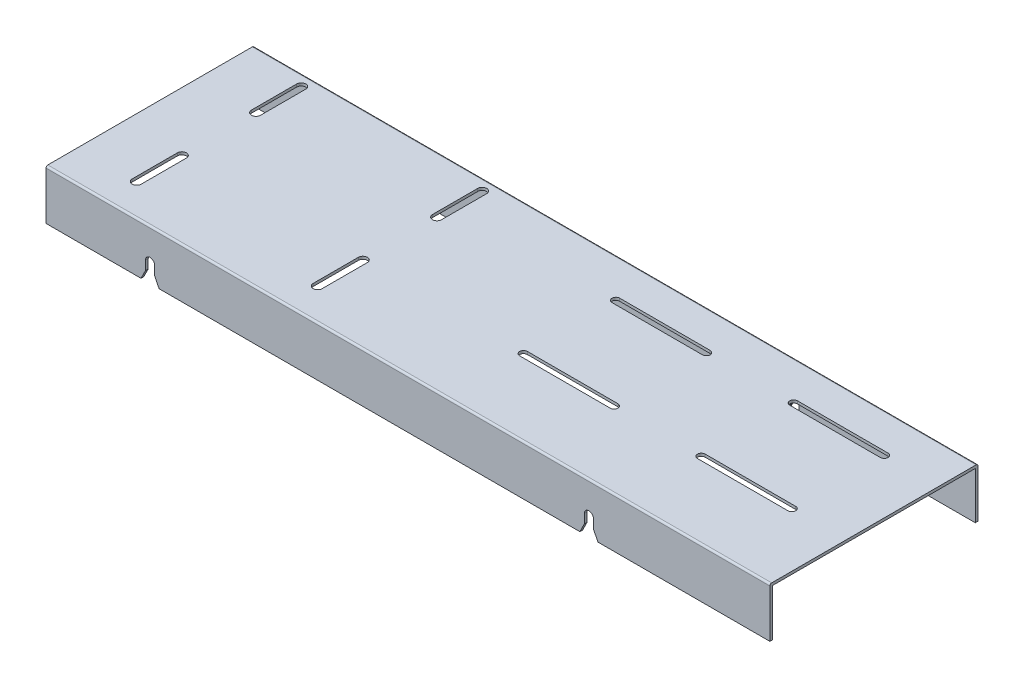
SolidWorks part; units mm, degrees
ref_plane "Plan de face" through (0, 0, 0) normal (0, 0, 1) x (1, 0, 0)
ref_plane "Plan de dessus" through (0, 0, 0) normal (0, 1, 0) x (1, 0, 0)
ref_plane "Plan de droite" through (0, 0, 0) normal (1, 0, 0) x (0, 0, -1)
sketch "Esquisse1" plane through (0, 0, 0) normal (1, 0, 0) x (0, 0, -1)
  line L0 (0, 0) -> (230, 0)
  line L1 (230, 0) -> (230, -55)
  line L2 (230, -55) -> (227, -55)
  line L3 (227, -55) -> (227, -3)
  line L4 (227, -3) -> (3, -3)
  line L5 (3, -3) -> (3, -55)
  line L6 (3, -55) -> (0, -55)
  line L7 (0, -55) -> (0, 0)
  dimension "D1" = 224
  dimension "D2" = 3
  dimension "D3" = 3
  dimension "D4" = 3
  dimension "D5" = 55
  dimension "D6" = 55
extrude "Boss.-Extru.1" add sketch "Esquisse1" along normal blind 800
sketch "Esquisse2" plane through (0, 0, 0) normal (0, 1, 0) x (1, 0, 0)
  line L0 (443.5, 186.25) -> (543.5, 186.25) construction
  line L1 (443.5, 190.5) -> (543.5, 190.5)
  line L2 (443.5, 182) -> (543.5, 182)
  line L3 (640, 186.25) -> (740, 186.25) construction
  line L4 (640, 190.5) -> (740, 190.5)
  line L5 (640, 182) -> (740, 182)
  line L6 (443.5, 84.25) -> (543.5, 84.25) construction
  line L7 (443.5, 88.5) -> (543.5, 88.5)
  line L8 (443.5, 80) -> (543.5, 80)
  line L9 (640, 84.25) -> (740, 84.25) construction
  line L10 (640, 88.5) -> (740, 88.5)
  line L11 (640, 80) -> (740, 80)
  line L12 (800, 230) -> (800, 0) construction
  line L13 (800, 0) -> (0, 0) construction
  arc A0 (443.5, 190.5) -> (443.5, 182) centre (443.5, 186.25) ccw
  arc A1 (543.5, 182) -> (543.5, 190.5) centre (543.5, 186.25) ccw
  arc A2 (640, 190.5) -> (640, 182) centre (640, 186.25) ccw
  arc A3 (740, 182) -> (740, 190.5) centre (740, 186.25) ccw
  arc A4 (443.5, 88.5) -> (443.5, 80) centre (443.5, 84.25) ccw
  arc A5 (543.5, 80) -> (543.5, 88.5) centre (543.5, 84.25) ccw
  arc A6 (640, 88.5) -> (640, 80) centre (640, 84.25) ccw
  arc A7 (740, 80) -> (740, 88.5) centre (740, 84.25) ccw
  point P2 (493.5, 186.25)
  point P7 (690, 186.25)
  point P14 (493.5, 84.25)
  point P21 (690, 84.25)
  dimension "D1" = 4.25
  dimension "D8" = 4.25
  dimension "D9" = 4.25
  dimension "D2" = 4.25
  dimension "D3" = 100
  dimension "D4" = 100
  dimension "D5" = 100
  dimension "D6" = 100
  dimension "D7" = 196.5
  dimension "D10" = 196.5
  dimension "D11" = 196.5
  dimension "D12" = 196.5
  dimension "D13" = 60
  dimension "D14" = 60
  dimension "D15" = 80
  dimension "D16" = 186.25
extrude "Enlèv. mat.-Extru.1" cut sketch "Esquisse2" against normal blind 30
sketch "Esquisse3" plane through (0, 0, 0) normal (0, 1, 0) x (1, 0, 0)
  line L0 (65, 217.1) -> (65, 167.1) construction
  line L1 (70, 217.1) -> (70, 167.1)
  line L2 (60, 217.1) -> (60, 167.1)
  line L3 (265, 217.1) -> (265, 167.1) construction
  line L4 (270, 217.1) -> (270, 167.1)
  line L5 (260, 217.1) -> (260, 167.1)
  line L6 (265, 85.2) -> (265, 35.2) construction
  line L7 (270, 85.2) -> (270, 35.2)
  line L8 (260, 85.2) -> (260, 35.2)
  line L9 (65, 35.2) -> (65, 85.2) construction
  line L10 (60, 35.2) -> (60, 85.2)
  line L11 (70, 35.2) -> (70, 85.2)
  line L12 (0, 230) -> (0, 0) construction
  line L13 (800, 0) -> (0, 0) construction
  arc A0 (70, 217.1) -> (60, 217.1) centre (65, 217.1) ccw
  arc A1 (60, 167.1) -> (70, 167.1) centre (65, 167.1) ccw
  arc A2 (270, 217.1) -> (260, 217.1) centre (265, 217.1) ccw
  arc A3 (260, 167.1) -> (270, 167.1) centre (265, 167.1) ccw
  arc A4 (270, 85.2) -> (260, 85.2) centre (265, 85.2) ccw
  arc A5 (260, 35.2) -> (270, 35.2) centre (265, 35.2) ccw
  arc A6 (60, 35.2) -> (70, 35.2) centre (65, 35.2) ccw
  arc A7 (70, 85.2) -> (60, 85.2) centre (65, 85.2) ccw
  point P2 (65, 192.1)
  point P7 (265, 192.1)
  point P14 (265, 60.2)
  point P21 (65, 60.2)
  dimension "D1" = 5
  dimension "D2" = 5
  dimension "D3" = 5
  dimension "D4" = 5
  dimension "D5" = 190
  dimension "D6" = 60
  dimension "D7" = 35.2
  dimension "D8" = 35.2
  dimension "D9" = 131.9
  dimension "D10" = 131.9
  dimension "D11" = 50
  dimension "D12" = 50
  dimension "D13" = 50
  dimension "D14" = 50
extrude "Enlèv. mat.-Extru.2" cut sketch "Esquisse3" against normal blind 30
sketch "Esquisse6" plane through (0, 0, 0) normal (0, 0, 1) x (1, 0, 0)
  line L0 (800, -55) -> (0, -55) construction
  line L1 (595, -55) -> (605, -55)
  line L2 (595, -45) -> (595, -35)
  line L4 (605, -45) -> (605, -35)
  line L5 (800, 0) -> (800, -55) construction
  line L6 (110, -45) -> (105, -55)
  line L7 (110, -55) -> (120, -55)
  line L8 (110, -45) -> (110, -35)
  line L10 (120, -45) -> (120, -35)
  line L11 (105, -55) -> (110, -55)
  line L12 (120, -45) -> (125, -55)
  line L13 (125, -55) -> (120, -55)
  line L14 (595, -45) -> (590, -55)
  line L15 (590, -55) -> (595, -55)
  line L16 (605, -45) -> (610, -55)
  line L17 (610, -55) -> (605, -55)
  arc A0 (605, -35) -> (595, -35) centre (600, -35) ccw
  arc A1 (120, -35) -> (110, -35) centre (115, -35) ccw
  dimension "D1" = 10
  dimension "D2" = 20
  dimension "D3" = 195
  dimension "D4" = 10
  dimension "D5" = 475
  dimension "D6" = 20
  dimension "D7" = 5
  dimension "D8" = 5
  dimension "D9" = 5
  dimension "D10" = 5
extrude "Enlèv. mat.-Extru.4" cut sketch "Esquisse6" against normal blind 300
fillet "Congé1" radius 2 2 edges at (400, 0, 0) (400, 0, -230)
